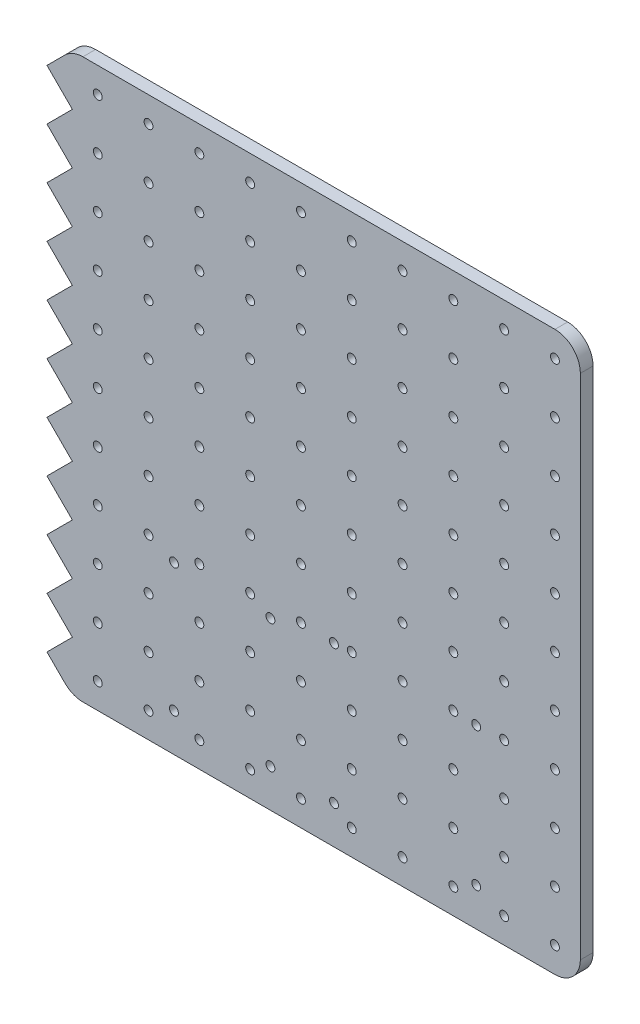
SolidWorks part; units mm, degrees
ref_plane "Front Plane" through (0, 0, 0) normal (0, 0, 1) x (1, 0, 0)
ref_plane "Top Plane" through (0, 0, 0) normal (0, 1, 0) x (1, 0, 0)
ref_plane "Right Plane" through (0, 0, 0) normal (1, 0, 0) x (0, 0, -1)
sketch "Sketch1" plane through (0, 0, 0) normal (0, 0, 1) x (1, 0, 0)
  line L0 (0, 0) -> (-10, 10)
  line L1 (0, 0) -> (200, 0)
  line L3 (0, 220) -> (200, 220)
  line L4 (200, 0) -> (200, 220)
  line L6 (-10, 10) -> (0, 20)
  line L7 (0, 20) -> (-10, 30)
  line L8 (-10, 30) -> (0, 40)
  line L9 (0, 40) -> (-10, 50)
  line L10 (-10, 50) -> (0, 60)
  line L11 (0, 60) -> (-10, 70)
  line L12 (-10, 70) -> (0, 80)
  line L13 (0, 80) -> (-10, 90)
  line L14 (-10, 90) -> (0, 100)
  line L15 (0, 100) -> (-10, 110)
  line L16 (-10, 110) -> (0, 120)
  line L17 (0, 120) -> (-10, 130)
  line L18 (-10, 130) -> (0, 140)
  line L19 (0, 140) -> (-10, 150)
  line L20 (-10, 150) -> (0, 160)
  line L21 (0, 160) -> (-10, 170)
  line L22 (-10, 170) -> (0, 180)
  line L23 (0, 180) -> (-10, 190)
  line L24 (-10, 190) -> (0, 200)
  line L25 (0, 200) -> (-10, 210)
  line L26 (-10, 210) -> (0, 220)
  circle A0 centre (190, 210) radius 1.75
  circle A1 centre (190, 190) radius 1.75
  circle A2 centre (190, 170) radius 1.75
  circle A3 centre (190, 150) radius 1.75
  circle A4 centre (190, 130) radius 1.75
  circle A5 centre (190, 110) radius 1.75
  circle A6 centre (190, 90) radius 1.75
  circle A7 centre (190, 70) radius 1.75
  circle A8 centre (190, 50) radius 1.75
  circle A9 centre (190, 30) radius 1.75
  circle A10 centre (190, 10) radius 1.75
  circle A11 centre (170, 210) radius 1.75
  circle A12 centre (170, 190) radius 1.75
  circle A13 centre (170, 170) radius 1.75
  circle A14 centre (170, 150) radius 1.75
  circle A15 centre (170, 130) radius 1.75
  circle A16 centre (150, 130) radius 1.75
  circle A17 centre (150, 150) radius 1.75
  circle A18 centre (150, 170) radius 1.75
  circle A19 centre (150, 190) radius 1.75
  circle A20 centre (150, 210) radius 1.75
  circle A21 centre (130, 210) radius 1.75
  circle A22 centre (130, 190) radius 1.75
  circle A23 centre (130, 170) radius 1.75
  circle A24 centre (130, 150) radius 1.75
  circle A25 centre (130, 130) radius 1.75
  circle A26 centre (110, 130) radius 1.75
  circle A27 centre (110, 150) radius 1.75
  circle A28 centre (110, 170) radius 1.75
  circle A29 centre (110, 190) radius 1.75
  circle A30 centre (110, 210) radius 1.75
  circle A31 centre (90, 210) radius 1.75
  circle A32 centre (90, 190) radius 1.75
  circle A33 centre (90, 170) radius 1.75
  circle A34 centre (90, 150) radius 1.75
  circle A35 centre (90, 130) radius 1.75
  circle A36 centre (70, 130) radius 1.75
  circle A37 centre (70, 150) radius 1.75
  circle A38 centre (70, 170) radius 1.75
  circle A39 centre (70, 190) radius 1.75
  circle A40 centre (70, 210) radius 1.75
  circle A41 centre (50, 210) radius 1.75
  circle A42 centre (50, 190) radius 1.75
  circle A43 centre (50, 170) radius 1.75
  circle A44 centre (50, 150) radius 1.75
  circle A45 centre (50, 130) radius 1.75
  circle A46 centre (30, 130) radius 1.75
  circle A47 centre (30, 150) radius 1.75
  circle A48 centre (30, 170) radius 1.75
  circle A49 centre (30, 190) radius 1.75
  circle A50 centre (30, 210) radius 1.75
  circle A51 centre (10, 210) radius 1.75
  circle A52 centre (10, 190) radius 1.75
  circle A53 centre (10, 170) radius 1.75
  circle A54 centre (10, 150) radius 1.75
  circle A55 centre (10, 130) radius 1.75
  circle A56 centre (10, 10) radius 1.75
  circle A57 centre (10, 30) radius 1.75
  circle A58 centre (10, 50) radius 1.75
  circle A59 centre (10, 70) radius 1.75
  circle A60 centre (10, 90) radius 1.75
  circle A61 centre (10, 110) radius 1.75
  circle A62 centre (30, 110) radius 1.75
  circle A63 centre (30, 90) radius 1.75
  circle A64 centre (30, 70) radius 1.75
  circle A65 centre (30, 50) radius 1.75
  circle A66 centre (30, 30) radius 1.75
  circle A67 centre (30, 10) radius 1.75
  circle A68 centre (50, 10) radius 1.75
  circle A69 centre (70, 10) radius 1.75
  circle A70 centre (70, 30) radius 1.75
  circle A71 centre (50, 30) radius 1.75
  circle A72 centre (50, 50) radius 1.75
  circle A73 centre (50, 70) radius 1.75
  circle A74 centre (50, 90) radius 1.75
  circle A75 centre (50, 110) radius 1.75
  circle A76 centre (70, 110) radius 1.75
  circle A77 centre (70, 90) radius 1.75
  circle A78 centre (70, 70) radius 1.75
  circle A79 centre (70, 50) radius 1.75
  circle A80 centre (90, 10) radius 1.75
  circle A81 centre (90, 30) radius 1.75
  circle A82 centre (90, 50) radius 1.75
  circle A83 centre (90, 70) radius 1.75
  circle A84 centre (90, 90) radius 1.75
  circle A85 centre (110, 90) radius 1.75
  circle A86 centre (90, 110) radius 1.75
  circle A87 centre (110, 110) radius 1.75
  circle A88 centre (130, 110) radius 1.75
  circle A89 centre (150, 110) radius 1.75
  circle A90 centre (170, 110) radius 1.75
  circle A91 centre (170, 90) radius 1.75
  circle A92 centre (150, 90) radius 1.75
  circle A93 centre (130, 90) radius 1.75
  circle A94 centre (110, 70) radius 1.75
  circle A95 centre (130, 70) radius 1.75
  circle A96 centre (150, 70) radius 1.75
  circle A97 centre (170, 70) radius 1.75
  circle A98 centre (170, 50) radius 1.75
  circle A99 centre (150, 50) radius 1.75
  circle A100 centre (130, 50) radius 1.75
  circle A101 centre (110, 50) radius 1.75
  circle A102 centre (110, 30) radius 1.75
  circle A103 centre (110, 10) radius 1.75
  circle A104 centre (130, 10) radius 1.75
  circle A105 centre (130, 30) radius 1.75
  circle A106 centre (150, 10) radius 1.75
  circle A107 centre (150, 30) radius 1.75
  circle A108 centre (170, 10) radius 1.75
  circle A109 centre (170, 30) radius 1.75
  circle A110 centre (40, 65.5) radius 1.75
  circle A111 centre (40, 15) radius 1.75
  circle A112 centre (78, 15) radius 1.75
  circle A113 centre (78, 65.5) radius 1.75
  circle A114 centre (103, 69.5) radius 1.75
  circle A115 centre (103, 15) radius 1.75
  circle A116 centre (159, 15) radius 1.75
  circle A117 centre (159, 69.5) radius 1.75
  dimension "D24" = 3.5
  dimension "D25" = 3.5
  dimension "D26" = 3.5
  dimension "D11" = 3.5
  dimension "D1" = 200
  dimension "D2" = 220
  dimension "D3" = 38
  dimension "D4" = 50.5
  dimension "D5" = 56
  dimension "D6" = 54.5
  dimension "D7" = 10
extrude "Boss-Extrude1" add sketch "Sketch1" along normal blind 5
fillet "Fillet1" radius 10 4 edges at (0, 0, 2.5) (200, 0, 2.5) (0, 220, 2.5) (200, 220, 2.5)
